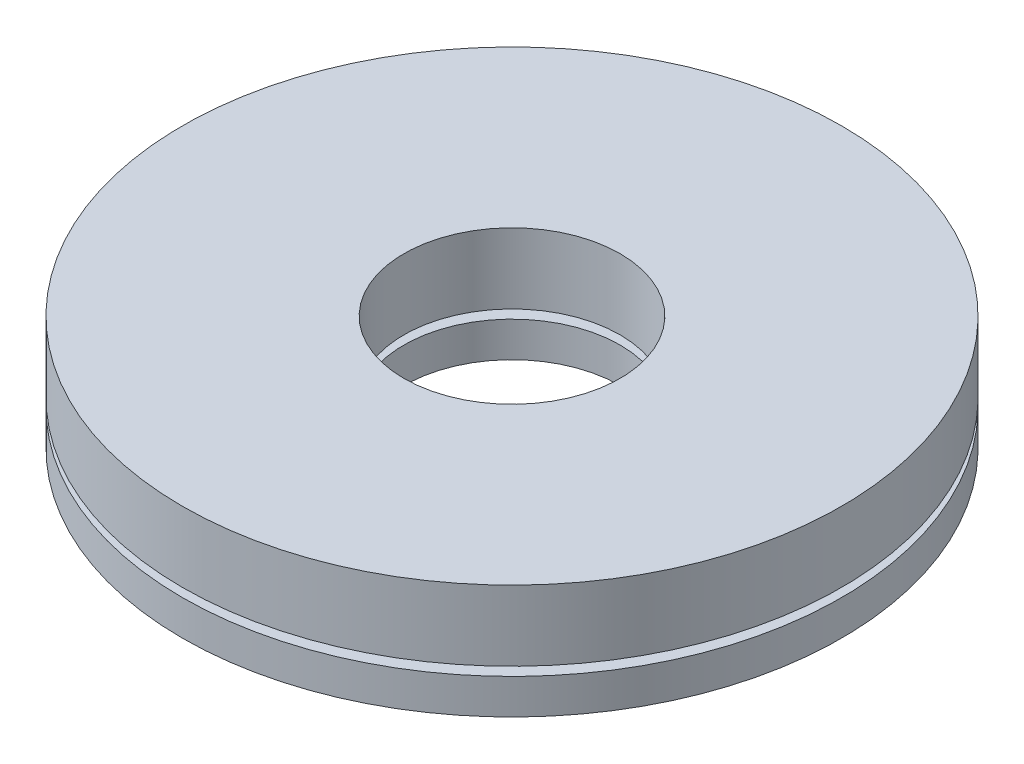
SolidWorks part; units mm, degrees
ref_plane "Front Plane" through (0, 0, 0) normal (0, 0, 1) x (1, 0, 0)
ref_plane "Top Plane" through (0, 0, 0) normal (0, 1, 0) x (1, 0, 0)
ref_plane "Right Plane" through (0, 0, 0) normal (1, 0, 0) x (0, 0, -1)
sketch "Sketch1" plane through (0, 0, 0) normal (0, 1, 0) x (1, 0, 0)
  circle A0 centre (0, 0) radius 9.375
  circle A1 centre (0, 0) radius 3.075
  dimension "D1" = 18.75
  dimension "D2" = 6.15
extrude "Boss-Extrude1" add sketch "Sketch1" along normal mid plane 2
ref_plane "Plane1" through (0, -1.25, 0) normal (0, -1, 0) x (-1, 0, 0)
sketch "Sketch2" plane through (0, -1.25, 0) normal (0, -1, 0) x (-1, 0, 0)
  circle A0 centre (0, 0) radius 3.075 construction
  circle A1 centre (0, 0) radius 9.375 construction
  circle A2 centre (0, 0) radius 3.075
  circle A3 centre (0, 0) radius 9.375
extrude "Boss-Extrude2" add sketch "Sketch2" along normal blind 1 separate body
